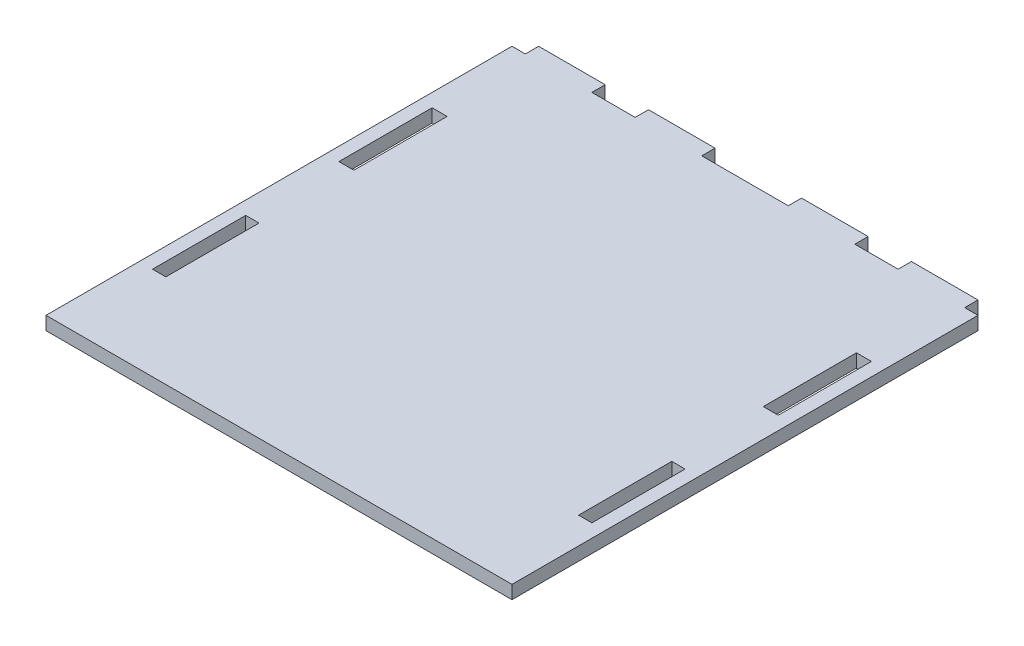
SolidWorks part; units mm, degrees
ref_plane "Front Plane" through (0, 0, 0) normal (0, 0, 1) x (1, 0, 0)
ref_plane "Top Plane" through (0, 0, 0) normal (0, 1, 0) x (1, 0, 0)
ref_plane "Right Plane" through (0, 0, 0) normal (1, 0, 0) x (0, 0, -1)
sketch "Sketch1" plane through (0, 0, 0) normal (0, 1, 0) x (1, 0, 0)
  line L0 (16.4159, 61.9469) -> (16.4159, -148.0531) construction
  line L2 (-88.5841, 61.9469) -> (-88.5841, -148.0531)
  line L4 (121.4159, 61.9469) -> (121.4159, -148.0531)
  line L5 (-88.5841, -43.0531) -> (121.4159, -43.0531) construction
  line L6 (-88.5841, 61.9469) -> (-82.5841, 61.9469)
  line L7 (-82.5841, 67.9469) -> (-82.5841, 61.9469)
  line L8 (-82.5841, 67.9469) -> (-52.5841, 67.9469)
  line L9 (-52.5841, 67.9469) -> (-52.5841, 61.9469)
  line L10 (-52.5841, 61.9469) -> (-33.0841, 61.9469)
  line L11 (-33.0841, 61.9469) -> (-33.0841, 67.9469)
  line L12 (-33.0841, 67.9469) -> (-3.0841, 67.9469)
  line L13 (-3.0841, 67.9469) -> (-3.0841, 61.9469)
  line L14 (-3.0841, 61.9469) -> (35.9159, 61.9469)
  line L15 (35.9159, 67.9469) -> (35.9159, 61.9469)
  line L16 (65.9159, 67.9469) -> (35.9159, 67.9469)
  line L17 (65.9159, 61.9469) -> (65.9159, 67.9469)
  line L18 (85.4159, 61.9469) -> (65.9159, 61.9469)
  line L19 (85.4159, 67.9469) -> (85.4159, 61.9469)
  line L20 (115.4159, 67.9469) -> (85.4159, 67.9469)
  line L21 (115.4159, 67.9469) -> (115.4159, 61.9469)
  line L22 (121.4159, 61.9469) -> (115.4159, 61.9469)
  line L40 (-82.5841, -22.0531) -> (-75.8255, -22.0531)
  line L41 (-82.5841, -106.0531) -> (-76.5841, -106.0531)
  line L42 (-82.5841, -106.0531) -> (-82.5841, -64.0531)
  line L43 (-82.5841, -64.0531) -> (-76.5841, -64.0531)
  line L44 (-76.5841, -106.0531) -> (-76.5841, -64.0531)
  line L45 (-82.5841, -22.0531) -> (-82.5841, 19.9469)
  line L46 (-82.5841, 19.9469) -> (-75.8255, 19.9469)
  line L47 (-75.8255, -22.0531) -> (-75.8255, 19.9469)
  line L48 (115.4159, -22.0531) -> (115.4159, 19.9469)
  line L49 (115.4159, 19.9469) -> (108.6574, 19.9469)
  line L50 (108.6574, -22.0531) -> (108.6574, 19.9469)
  line L51 (115.4159, -22.0531) -> (108.6574, -22.0531)
  line L52 (115.4159, -64.0531) -> (109.4159, -64.0531)
  line L53 (109.4159, -106.0531) -> (109.4159, -64.0531)
  line L54 (115.4159, -106.0531) -> (109.4159, -106.0531)
  line L55 (115.4159, -106.0531) -> (115.4159, -64.0531)
  line L56 (-88.5841, -148.0531) -> (121.4159, -148.0531)
  dimension "D1" = 210
  dimension "D2" = 210
  dimension "D3" = 6
  dimension "D4" = 30
  dimension "D5" = 19.5
  dimension "D6" = 6
  dimension "D7" = 6
  dimension "D8" = 30
  dimension "D9" = 42
  dimension "D10" = 6
  dimension "D12" = 42
  dimension "D13" = 42
  dimension "D14" = 6
extrude "Boss-Extrude1" add sketch "Sketch1" along normal blind 6
